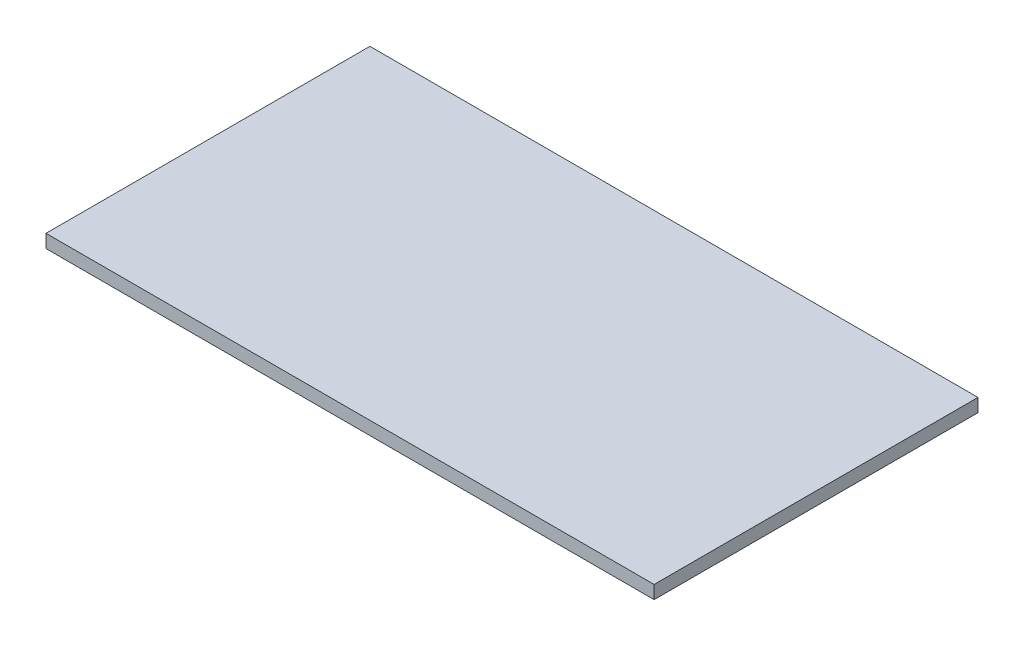
SolidWorks part; units mm, degrees
material "Oak"
ref_plane "Front Plane" through (0, 0, 0) normal (0, 0, 1) x (1, 0, 0)
ref_plane "Top Plane" through (0, 0, 0) normal (0, 1, 0) x (1, 0, 0)
ref_plane "Right Plane" through (0, 0, 0) normal (1, 0, 0) x (0, 0, -1)
sketch "Sketch1" plane through (0, 0, 0) normal (0, 1, 0) x (1, 0, 0)
  line L1 (-438.15, -233.3625) -> (438.15, -233.3625)
  line L2 (-438.15, -233.3625) -> (-438.15, 233.3625)
  line L3 (-438.15, 233.3625) -> (438.15, 233.3625)
  line L4 (438.15, -233.3625) -> (438.15, 233.3625)
  line L5 (-438.15, -233.3625) -> (438.15, 233.3625) construction
  line L6 (-438.15, 233.3625) -> (438.15, -233.3625) construction
  point P0 (0, 0)
  dimension "D1" = 876.3
  dimension "D2" = 466.725
extrude "Boss-Extrude1" add sketch "Sketch1" along normal blind 19.05
